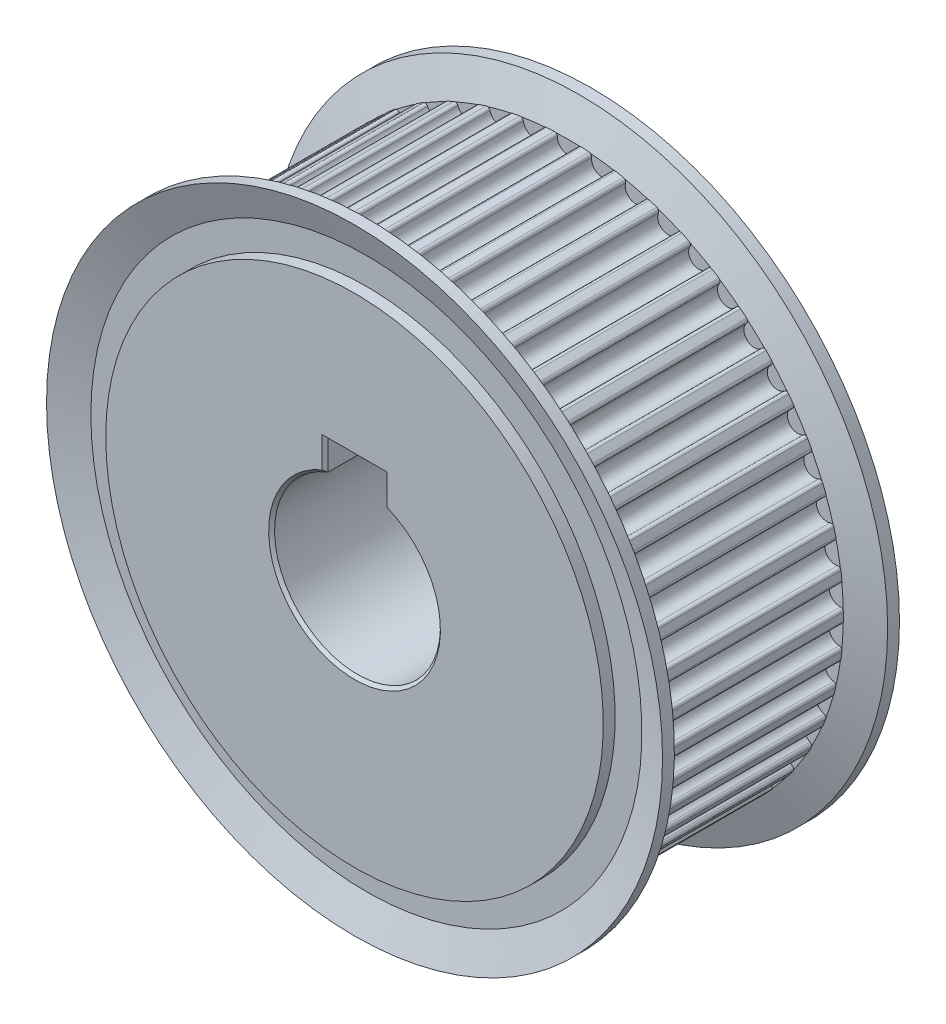
SolidWorks part; units mm, degrees
ref_plane "Front Plane" through (0, 0, 0) normal (0, 0, 1) x (1, 0, 0)
ref_plane "Top Plane" through (0, 0, 0) normal (0, 1, 0) x (1, 0, 0)
ref_plane "Right Plane" through (0, 0, 0) normal (1, 0, 0) x (0, 0, -1)
sketch "Sketch1" plane through (0, 0, 0) normal (0, 0, 1) x (1, 0, 0)
  circle A0 centre (0, 0) radius 23.875
  dimension "D1" = 47.75
extrude "Base" add sketch "Sketch1" against normal mid plane 16
sketch "Sketch2" plane through (0, 0, 0) normal (0, 0, 1) x (1, 0, 0)
  line L0 (0, 0) -> (-1.4612, 23.2391) construction
  line L1 (0, 0) -> (1.4629, 23.239) construction
  line L2 (0, 0) -> (0, 23.875) construction
  line L3 (-1.4612, 23.2391) -> (-1.4982, 23.8279)
  line L4 (1.4629, 23.239) -> (1.5, 23.8278)
  circle A0 centre (0, 0) radius 23.875 construction
  arc A1 (1.5, 23.8278) -> (-1.4982, 23.8279) centre (0, 0) ccw
  arc A2 (-1.1319, 23.2575) -> (-1.4612, 23.2391) centre (0, 0) ccw
  arc A3 (-0.8698, 23.0027) -> (0.8698, 23.0027) centre (0, 22.985) ccw
  arc A4 (-0.8698, 23.0027) -> (-1.1319, 23.2575) centre (-1.1198, 23.0078) ccw
  arc A5 (1.1319, 23.2575) -> (0.8698, 23.0027) centre (1.1198, 23.0078) ccw
  arc A6 (1.4629, 23.239) -> (1.1319, 23.2575) centre (0, 0) ccw
  dimension "D3" = 46.57
  dimension "D4" = 1.74
  dimension "D5" = 0.5
  dimension "D1" = 7.2
  dimension "D2" = 1.5
  dimension "D6" = 0.89
extrude "ToothCut" cut sketch "Sketch2" against normal through all both and the other way through all
pattern_circular "TeethCuts" count 50 over 360 about axis through (0, 0, 0) along (0, 0, 1) of "ToothCut"
sketch "Sketch6" plane through (0, 0, 0) normal (1, 0, 0) x (0, 0, -1)
  line L0 (-8, 23.2575) -> (-9, 26)
  line L1 (-9, 26) -> (-10, 26)
  line L2 (-10, 26) -> (-9, 23.2575)
  line L3 (-9, 23.2575) -> (-9, 21)
  line L4 (-9, 21) -> (-10, 21)
  line L5 (-10, 21) -> (-10, 0)
  line L6 (-10, 0) -> (-8, 0)
  line L7 (-8, 0.3307) -> (-8, -0.3307) construction
  line L8 (-8, 0) -> (-8, 23.2575)
  line L9 (0, 23.2575) -> (0, -23.2575) construction
  line L10 (8, 23.2575) -> (-8, 23.2575) construction
  line L11 (8, -23.2575) -> (-8, -23.2575) construction
  line L12 (8, 0) -> (8, 23.2575)
  line L13 (10, 0) -> (8, 0)
  line L14 (10, 21) -> (10, 0)
  line L15 (9, 21) -> (10, 21)
  line L16 (9, 23.2575) -> (9, 21)
  line L17 (10, 26) -> (9, 23.2575)
  line L18 (9, 26) -> (10, 26)
  line L19 (8, 23.2575) -> (9, 26)
  point P25 (8.5, 24.6287)
  point P26 (-8.5, 24.6287)
  dimension "D1" = 17
  dimension "D2" = 20
  dimension "D3" = 26
  dimension "D4" = 21
revolve "Flange" add sketch "Sketch6" angle 360 about axis through (0, 0, -8) along (0, 0, 1)
sketch "Sketch7" plane through (0, 0, 0) normal (0, 0, 1) x (1, 0, 0)
  line L0 (-2.485, 9.0441) -> (2.485, 9.0441)
  line L1 (2.485, 9.0441) -> (2.485, 6.5441)
  line L2 (-2.485, 9.0441) -> (-2.485, 6.5441)
  arc A0 (-2.485, 6.5441) -> (2.485, 6.5441) centre (0, 0) ccw
  point P8 (0, 9.0441)
  dimension "D2" = 14
  dimension "D1" = 4.97
  dimension "D3" = 2.5
extrude "Bore and Keyway" cut sketch "Sketch7" against normal through all both and the other way through all
chamfer "BoreChamfer" distance 0.25 angle 45 8 edges at (0, -7, 10) (2.485, 7.7941, -10) (0, 9.0441, -10) (-2.485, 7.7941, -10) (0, -7, -10) (-2.485, 7.7941, 10) (0, 9.0441, 10) (2.485, 7.7941, 10)
equation "\"N\"= 50'Number of teeth"
equation "\"P\"= 3'Pitch length"
equation "\"DP\"= ( \"N\" * \"P\" ) / ( PI )'Pitch circle diameter"
equation "\"R\"= 0.87"
equation "\"R2\"= 0.25"
equation "\"B\"= 2.40"
equation "\"T\"= 1.22"
equation "\"Tooth angle\"= ( 360 / \"N\" )"
